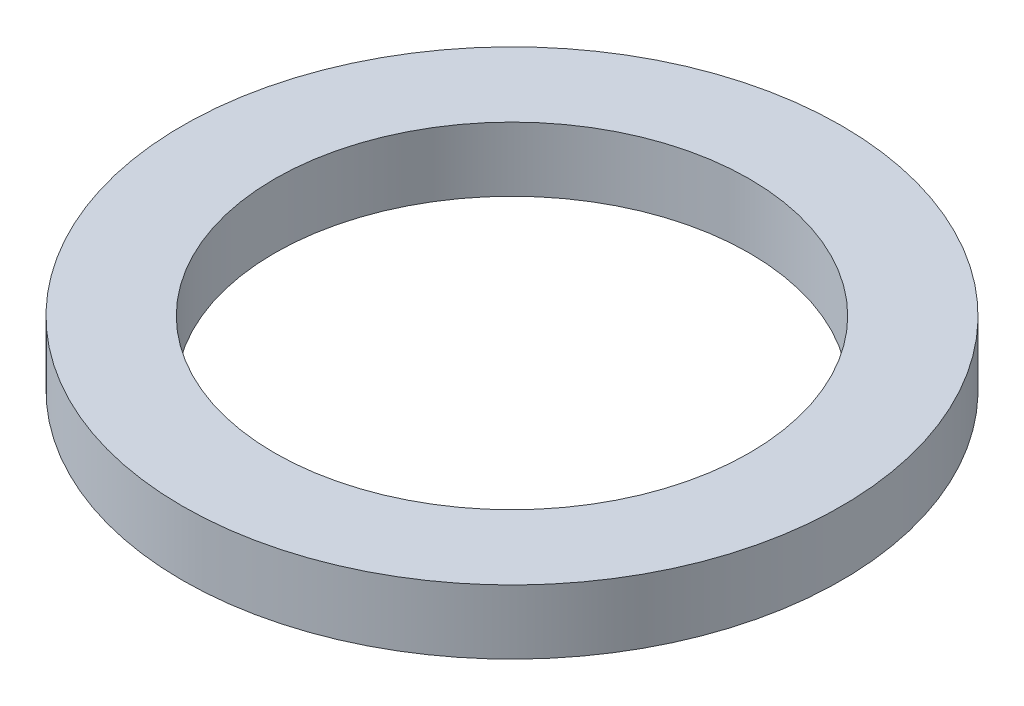
SolidWorks part; units mm, degrees
material "AISI 304"
ref_plane "Front Plane" through (0, 0, 0) normal (0, 0, 1) x (1, 0, 0)
ref_plane "Top Plane" through (0, 0, 0) normal (0, 1, 0) x (1, 0, 0)
ref_plane "Right Plane" through (0, 0, 0) normal (1, 0, 0) x (0, 0, -1)
sketch "Sketch1" plane through (0, 0, 0) normal (0, 1, 0) x (1, 0, 0)
  circle A0 centre (0, 0) radius 5.9
  circle A1 centre (0, 0) radius 4.25
  dimension "D1" = 8.5
  dimension "D2" = 11.8
extrude "Boss-Extrude1" add sketch "Sketch1" along normal blind 1.15
